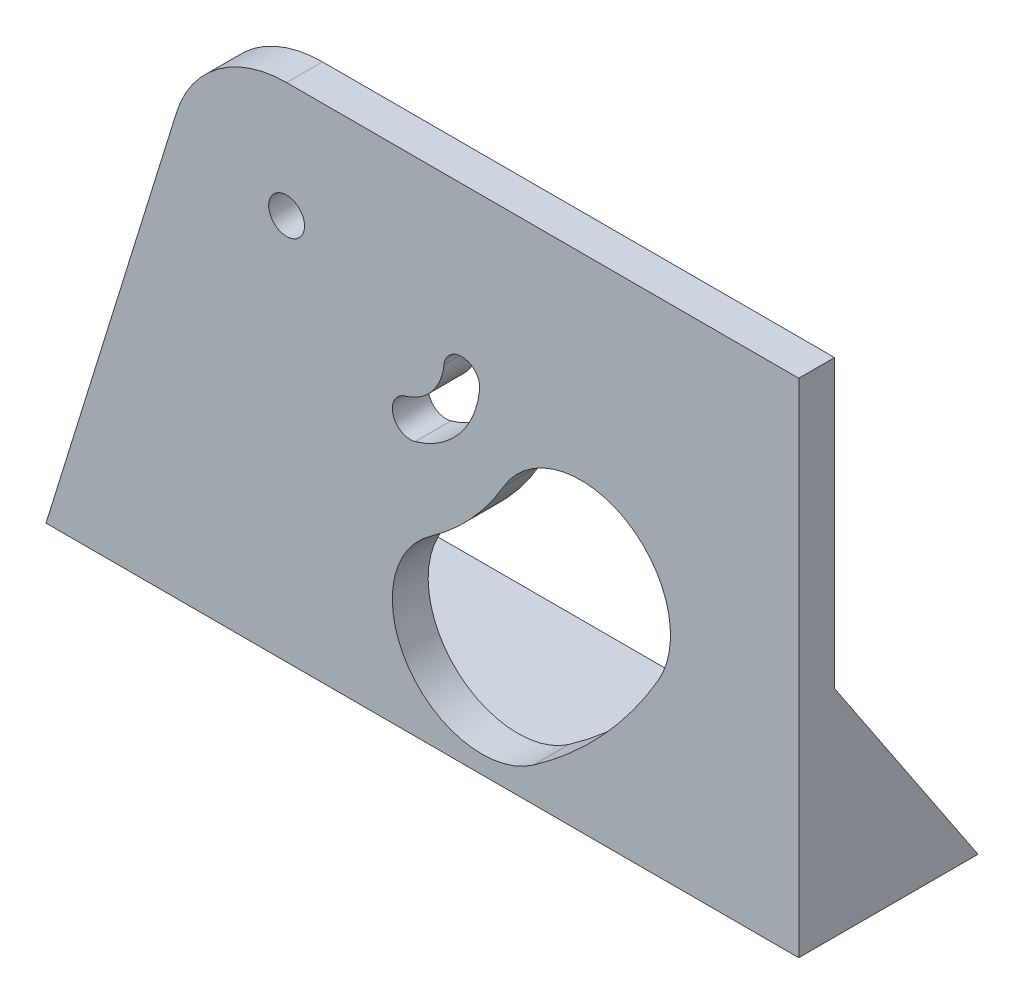
SolidWorks part; units mm, degrees
ref_plane "Front Plane" through (0, 0, 0) normal (0, 0, 1) x (1, 0, 0)
ref_plane "Top Plane" through (0, 0, 0) normal (0, 1, 0) x (1, 0, 0)
ref_plane "Right Plane" through (0, 0, 0) normal (1, 0, 0) x (0, 0, -1)
sketch "Sketch1" plane through (0, 0, 0) normal (0, 0, 1) x (1, 0, 0)
  line L1 (0, 0) -> (120, 0)
  line L2 (0, 0) -> (0, 100)
  line L3 (0, 100) -> (120, 100)
  line L4 (120, 0) -> (120, 100)
  dimension "D1" = 120
  dimension "D2" = 100
extrude "Boss-Extrude1" add sketch "Sketch1" along normal blind 5
sketch "Sketch2" plane through (0, 0, 5) normal (0, 0, 1) x (1, 0, 0)
  line L0 (0, 0) -> (120, 0) construction
  line L3 (82.976, 4.7606) -> (120, 30.6851) construction
  line L4 (120, 0) -> (120, 100) construction
  arc A0 (75.8063, 15) -> (89.605, 30) centre (48.5614, 53.9097) ccw construction
  arc A1 (82.976, 4.7606) -> (100.4059, 23.708) centre (48.5614, 53.9097) ccw
  arc A2 (68.6366, 25.2394) -> (78.804, 36.292) centre (48.5614, 53.9097) ccw
  arc A3 (68.6366, 25.2394) -> (82.976, 4.7606) centre (75.8063, 15) ccw
  arc A4 (100.4059, 23.708) -> (78.804, 36.292) centre (89.605, 30) ccw
  arc A5 (48.5614, 6.4097) -> (89.605, 30) centre (48.5614, 53.9097) ccw construction
  arc A6 (48.5614, -28.5903) -> (119.8476, 12.3823) centre (48.5614, 53.9097) ccw construction
  arc A7 (48.5614, 41.4097) -> (59.3623, 47.6177) centre (48.5614, 53.9097) ccw construction
  arc A8 (48.5614, 41.4097) -> (48.5614, -28.5903) centre (48.5614, 6.4097) ccw construction
  arc A9 (119.8476, 12.3823) -> (59.3623, 47.6177) centre (89.605, 30) ccw construction
  circle A10 centre (48.5614, 53.9097) radius 2.5
  point P3 (83.5196, 21.7512)
  point P17 (72.2314, 12.7274)
  point P27 (115, 5)
  dimension "D1" = 47.5
  dimension "D3" = 12.5
  dimension "D6" = 5
  dimension "D5" = 35
  dimension "D9" = 5
  dimension "D2" = 15
  dimension "D4" = 30
  dimension "D7" = 5
  dimension "D8" = 35
extrude "Cut-Extrude1" cut sketch "Sketch2" against normal through all
sketch "Sketch3" plane through (0, 0, 0) normal (0, 0, -1) x (-1, 0, 0)
  line L0 (0, 100) -> (0, 0) construction
  line L1 (-120, 0) -> (0, 0)
  line L2 (-120, 0) -> (-120, 2)
  line L3 (-120, 2) -> (0, 2)
  line L4 (0, 0) -> (0, 2)
  dimension "D1" = 2
extrude "Boss-Extrude2" add sketch "Sketch3" along normal blind 20
sketch "Sketch4" plane through (0, 0, 5) normal (0, 0, 1) x (1, 0, 0)
  line L0 (89.605, 30) -> (48.5614, 53.9097) construction
  line L1 (48.5614, 53.9097) -> (75.8063, 15) construction
  line L2 (92.6251, 35.1845) -> (51.5816, 59.0942) construction
  line L3 (52.6571, 56.7776) -> (79.902, 17.8679) construction
  line L4 (120, 0) -> (120, 100) construction
  line L5 (0, 0) -> (120, 0) construction
  arc A0 (65.8054, 38) -> (73, 46.617) centre (63.0497, 47.6128) ccw construction
  arc A1 (66.4943, 35.5968) -> (75.4876, 46.368) centre (63.0497, 47.6128) ccw
  arc A2 (65.1165, 40.4032) -> (70.5124, 46.8659) centre (63.0497, 47.6128) ccw
  arc A3 (65.1165, 40.4032) -> (66.4943, 35.5968) centre (65.8054, 38) ccw
  arc A4 (75.4876, 46.368) -> (70.5124, 46.8659) centre (73, 46.617) ccw
  point P13 (70.7259, 41.2037)
  dimension "D3" = 2.5
  dimension "D4" = 10
  dimension "D5" = 47
  dimension "D6" = 38
  dimension "D1" = 6
  dimension "D2" = 5
extrude "Cut-Extrude2" cut sketch "Sketch4" against normal through all
sketch "Sketch5" plane through (0, 0, 5) normal (0, 0, 1) x (1, 0, 0)
  line L0 (120, 70) -> (48.5614, 70)
  line L1 (120, 0) -> (120, 100) construction
  line L2 (33.1929, 58.6749) -> (15, 0)
  line L3 (0, 0) -> (120, 0) construction
  line L4 (15, 0) -> (0, 0)
  line L5 (0, 0) -> (0, 100)
  line L6 (0, 100) -> (120, 100)
  line L7 (120, 100) -> (120, 70)
  arc A0 (48.5614, 70) -> (33.1929, 58.6749) centre (48.5614, 53.9097) ccw
  circle A1 centre (48.5614, 53.9097) radius 2.5 construction
  dimension "D1" = 15
  dimension "D2" = 70
extrude "Cut-Extrude3" cut sketch "Sketch5" against normal through all
sketch "Sketch6" plane through (0, 0, 0) normal (0, 0, -1) x (-1, 0, 0)
  line L0 (-120, 2) -> (-120, 70) construction
  line L1 (-120, 30) -> (-115, 30)
  line L2 (-120, 30) -> (-120, 0)
  line L3 (-120, 0) -> (-115, 0)
  line L4 (-115, 30) -> (-115, 0)
  line L5 (-120, 0) -> (-15, 0) construction
  line L7 (-35, 0) -> (-30, 0)
  line L8 (-35, 0) -> (-35, 30)
  line L9 (-35, 30) -> (-30, 30)
  line L10 (-30, 0) -> (-30, 30)
  dimension "D1" = 5
  dimension "D2" = 30
  dimension "D3" = 5
  dimension "D4" = 30
  dimension "D5" = 80
extrude "Boss-Extrude3" add sketch "Sketch6" along normal through all
sketch "Sketch9" plane through (120, 0, 0) normal (1, 0, 0) x (0, 0, -1)
  line L0 (0, 30) -> (20, 0)
  line L1 (20, 30) -> (0, 30) construction
  line L2 (20, 0) -> (20, 30)
  line L3 (20, 30) -> (0, 30)
extrude "Cut-Extrude4" cut sketch "Sketch9" against normal through all
